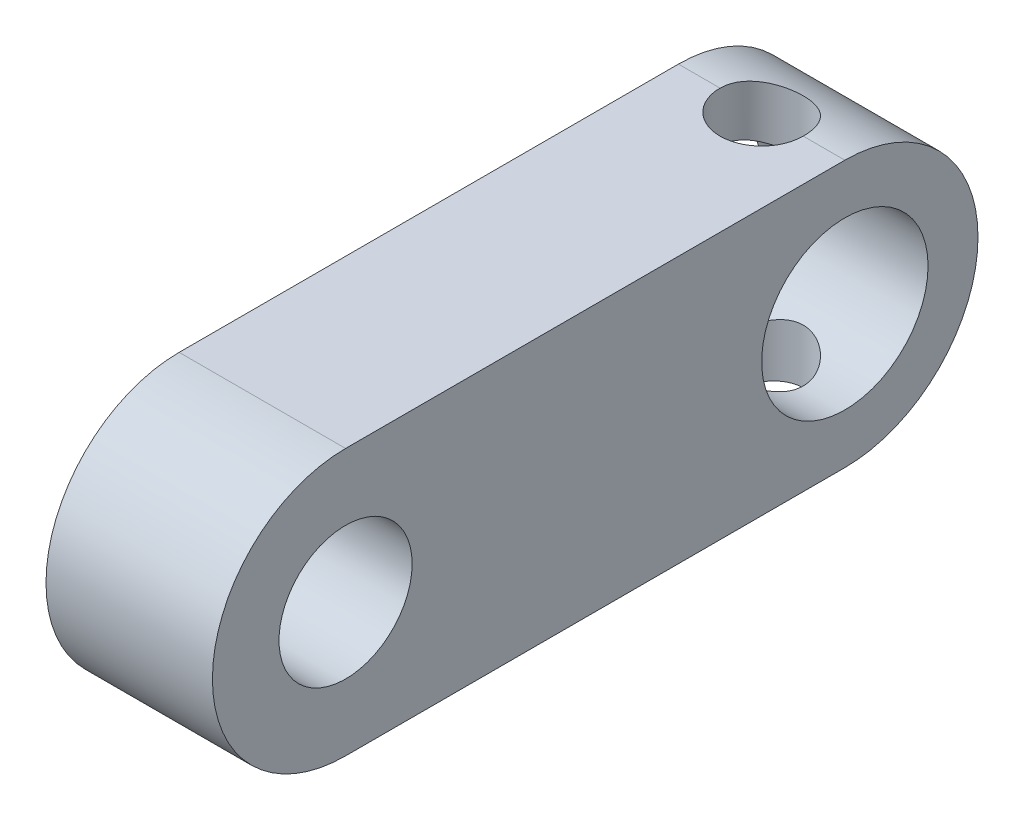
SolidWorks part; units mm, degrees
material "普通碳钢"
ref_plane "前视基准面" through (0, 0, 0) normal (0, 0, 1) x (1, 0, 0)
ref_plane "上视基准面" through (0, 0, 0) normal (0, 1, 0) x (1, 0, 0)
ref_plane "右视基准面" through (0, 0, 0) normal (1, 0, 0) x (0, 0, -1)
sketch "草图1" plane through (0, 0, 0) normal (1, 0, 0) x (0, 0, -1)
  line L0 (0, 28.2267) -> (0, -33.4957) construction
  line L1 (-74.8948, 0) -> (95.5944, 0) construction
  line L2 (15, 8) -> (-15, 8)
  line L3 (-15, -8) -> (15, -8)
  line L4 (74.8948, 0) -> (-95.5944, 0) construction
  arc A0 (-15, 8) -> (-15, -8) centre (-15, 0) ccw
  circle A1 centre (-15, 0) radius 4
  circle A2 centre (15, 0) radius 5
  arc A3 (15, 8) -> (15, -8) centre (15, 0) cw
  point P11 (0, 8)
  point P17 (0, -8)
  dimension "D1" = 8
  dimension "D2" = 8
  dimension "D4" = 10
  dimension "D3" = 30
extrude "凸台-拉伸1" add sketch "草图1" along normal blind 10
sketch3d "3D草图1"
  line L0 (-10.0611, 0, -15) -> (10, 0, -15) construction
  line L1 (10, 0, -15) -> (0, 0, -15) construction
sketch "草图2" plane through (0, 8, 0) normal (0, 1, 0) x (1, 0, 0)
  line L0 (5, 23) -> (5, 18.3538) construction
  line L1 (10, 23) -> (0, 23) construction
  line L2 (-10.0611, 15) -> (10, 15) construction
  circle A0 centre (5, 15) radius 2.5
  dimension "D1" = 5
extrude "切除-拉伸1" cut sketch "草图2" against normal through all
